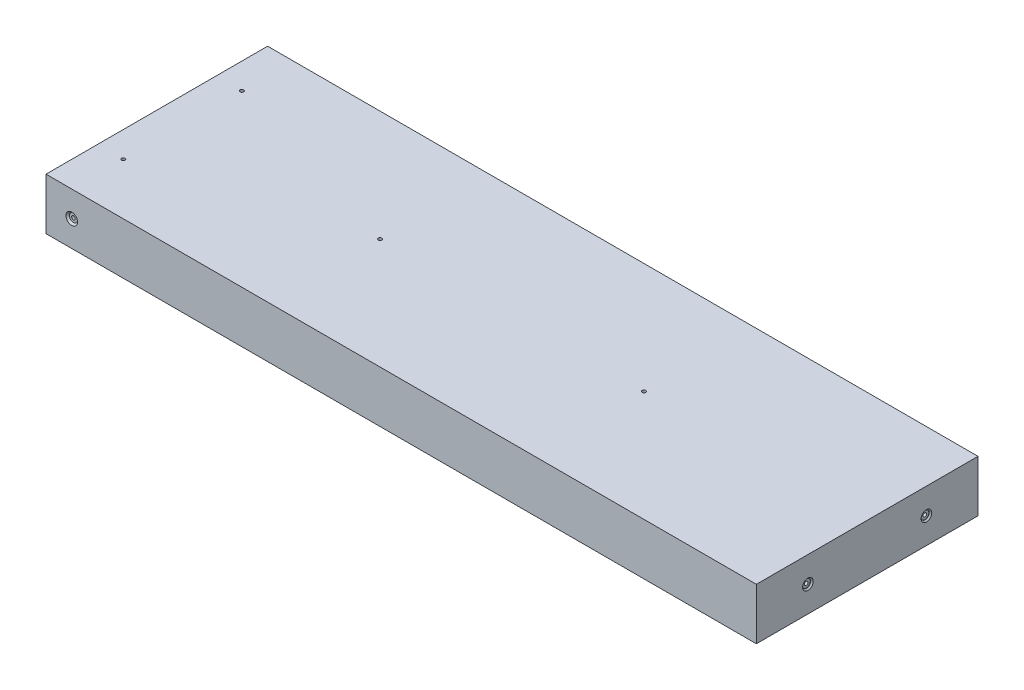
SolidWorks part; units mm, degrees
material "Balsa"
ref_plane "Front Plane" through (0, 0, 0) normal (0, 0, 1) x (1, 0, 0)
ref_plane "Top Plane" through (0, 0, 0) normal (0, 1, 0) x (1, 0, 0)
ref_plane "Right Plane" through (0, 0, 0) normal (1, 0, 0) x (0, 0, -1)
sketch "Sketch1" plane through (0, 0, 0) normal (0, 1, 0) x (1, 0, 0)
  line L1 (-175, 54.6) -> (175, 54.6)
  line L2 (-175, 54.6) -> (-175, -54.6)
  line L3 (-175, -54.6) -> (175, -54.6)
  line L4 (175, 54.6) -> (175, -54.6)
  line L5 (-175, 54.6) -> (175, -54.6) construction
  line L6 (-175, -54.6) -> (175, 54.6) construction
  point P0 (0, 0)
  dimension "D1" = 109.2
  dimension "D2" = 350
extrude "Boss-Extrude1" add sketch "Sketch1" along normal blind 25.4
hole_wizard "CBORE for #0 Binding Head Machine Screw1" positions "Sketch2" profile "Sketch3" counterbore size "#0" standard "ANSI Inch"
sketch "Sketch2" plane through (0, 0, 54.6) normal (0, 0, 1) x (1, 0, 0)
  line L0 (-175, 25.4) -> (-175, 0) construction
  line L1 (-175, 25.4) -> (175, 25.4) construction
  point P0 (-162.3, 12.7)
  dimension "D1" = 12.7
  dimension "D2" = 12.7
sketch "Sketch3" plane through (-162.3, 12.7, 54.6) normal (1, 0, 0) x (0, -1, 0)
  line L0 (0, 0) -> (0, 30.5342)
  line L1 (0, 30.5342) -> (0.889, 30)
  line L2 (0.889, 30) -> (0.889, 0.8128)
  line L3 (0.889, 0.8128) -> (1.985, 0.8128)
  line L5 (1.985, 0.8128) -> (1.985, 0.8725)
  line L6 (1.985, 0.8725) -> (2.8575, 0)
  line L7 (2.8575, 0) -> (0, 0)
  line L8 (-1.985, 0.8725) -> (-2.8575, 0) construction
  line L10 (0, 30.5342) -> (-0.889, 30) construction
  line L11 (0, -6.35) -> (0, 107.95) construction
  dimension "Hole Dia." = 1.778
  dimension "Hole Depth" = 30
  dimension "C'Bore Dia." = 3.97
  dimension "C'Bore Depth" = 0.8128
  dimension "Near C'Sink Dia." = 5.715
  dimension "Near C'Sink Angle" = 90
  dimension "Drill Angle" = 118
mirror "Mirror1" about plane through (0, 0, 0) normal (0, 0, 1) of "CBORE for #0 Binding Head Machine Screw1"
hole_wizard "CBORE for #0 Binding Head Machine Screw2" positions "Sketch4" profile "Sketch5" counterbore size "#0" standard "ANSI Inch"
sketch "Sketch4" plane through (175, 0, 0) normal (1, 0, 0) x (0, 0, -1)
  line L0 (-54.6, 25.4) -> (-54.6, 0) construction
  line L2 (-54.6, 25.4) -> (54.6, 25.4) construction
  point P0 (-29.1995, 12.7)
  point P2 (29.2005, 12.7)
  dimension "D1" = 58.4
  dimension "D2" = 25.4005
  dimension "D4" = 12.7
sketch "Sketch5" plane through (175, 12.7, 29.1995) normal (0, 1, 0) x (0, 0, -1)
  line L0 (0, 0) -> (0, 30.5342)
  line L1 (0, 30.5342) -> (0.889, 30)
  line L2 (0.889, 30) -> (0.889, 0.8128)
  line L3 (0.889, 0.8128) -> (1.985, 0.8128)
  line L5 (1.985, 0.8128) -> (1.985, 0.635)
  line L6 (1.985, 0.635) -> (2.62, 0)
  line L7 (2.62, 0) -> (0, 0)
  line L8 (-1.985, 0.635) -> (-2.62, 0) construction
  line L10 (0, 30.5342) -> (-0.889, 30) construction
  line L11 (0, -6.35) -> (0, 107.95) construction
  dimension "Hole Dia." = 1.778
  dimension "Hole Depth" = 30
  dimension "C'Bore Dia." = 3.97
  dimension "C'Bore Depth" = 0.8128
  dimension "Near C'Sink Dia." = 5.24
  dimension "Near C'Sink Angle" = 90
  dimension "Drill Angle" = 118
hole_wizard "CBORE for #0 Binding Head Machine Screw4" positions "Sketch8" profile "Sketch9" counterbore size "#0" standard "ANSI Inch"
sketch "Sketch8" plane through (0, 0, 0) normal (0, -1, 0) x (-1, 0, 0)
  line L0 (0, 54.6) -> (0, -54.6) construction
  line L1 (-175, 54.6) -> (175, 54.6) construction
  line L2 (175, -54.6) -> (-175, -54.6) construction
  line L4 (175, 0) -> (-175, 0) construction
  line L5 (175, 54.6) -> (175, -54.6) construction
  line L6 (-175, -54.6) -> (-175, 54.6) construction
  point P0 (65, 0)
  point P2 (-65, 0)
  dimension "D1" = 130
sketch "Sketch9" plane through (-65, 0, 0) normal (1, 0, 0) x (0, 0, -1)
  line L0 (0, 0) -> (0, 30.5342)
  line L1 (0, 30.5342) -> (0.889, 30)
  line L2 (0.889, 30) -> (0.889, 0.8128)
  line L3 (0.889, 0.8128) -> (1.985, 0.8128)
  line L5 (1.985, 0.8128) -> (1.985, 0.8725)
  line L6 (1.985, 0.8725) -> (2.8575, 0)
  line L7 (2.8575, 0) -> (0, 0)
  line L8 (-1.985, 0.8725) -> (-2.8575, 0) construction
  line L10 (0, 30.5342) -> (-0.889, 30) construction
  line L11 (0, -6.35) -> (0, 107.95) construction
  dimension "Hole Dia." = 1.778
  dimension "Hole Depth" = 30
  dimension "C'Bore Dia." = 3.97
  dimension "C'Bore Depth" = 0.8128
  dimension "Near C'Sink Dia." = 5.715
  dimension "Near C'Sink Angle" = 90
  dimension "Drill Angle" = 118
hole_wizard "CBORE for #0 Binding Head Machine Screw6" positions "Sketch12" profile "Sketch13" counterbore size "#0" standard "ANSI Inch" end condition through all
sketch "Sketch12" plane through (0, 0, 0) normal (0, -1, 0) x (-1, 0, 0)
  line L0 (175, 54.6) -> (175, -54.6) construction
  line L1 (-175, 54.6) -> (175, 54.6) construction
  point P0 (162.3, 29.2)
  point P2 (162.3, -29.2)
  dimension "D1" = 12.7
  dimension "D2" = 12.7
  dimension "D3" = 58.4
  dimension "D4" = 25.4
sketch "Sketch13" plane through (-162.3, 0, -29.2) normal (1, 0, 0) x (0, 0, -1)
  line L0 (0, 0) -> (0, 25.4)
  line L1 (0, 25.4) -> (0.889, 25.4)
  line L3 (0.889, 25.4) -> (0.889, 0.8128)
  line L4 (1.985, 0.8128) -> (0.889, 0.8128)
  line L5 (1.985, 0.8128) -> (1.985, 0.8725)
  line L6 (1.985, 0.8725) -> (2.8575, 0)
  line L7 (2.8575, 0) -> (0, 0)
  line L8 (-1.985, 0.8725) -> (-2.8575, 0) construction
  line L11 (0, -6.35) -> (0, 107.95) construction
  dimension "Thru Hole Dia." = 1.778
  dimension "Thru Hole Depth" = 25.4
  dimension "C'Bore Dia." = 3.97
  dimension "C'Bore Depth" = 0.8128
  dimension "Near C'Sink Dia." = 5.715
  dimension "Near C'Sink Angle" = 90
